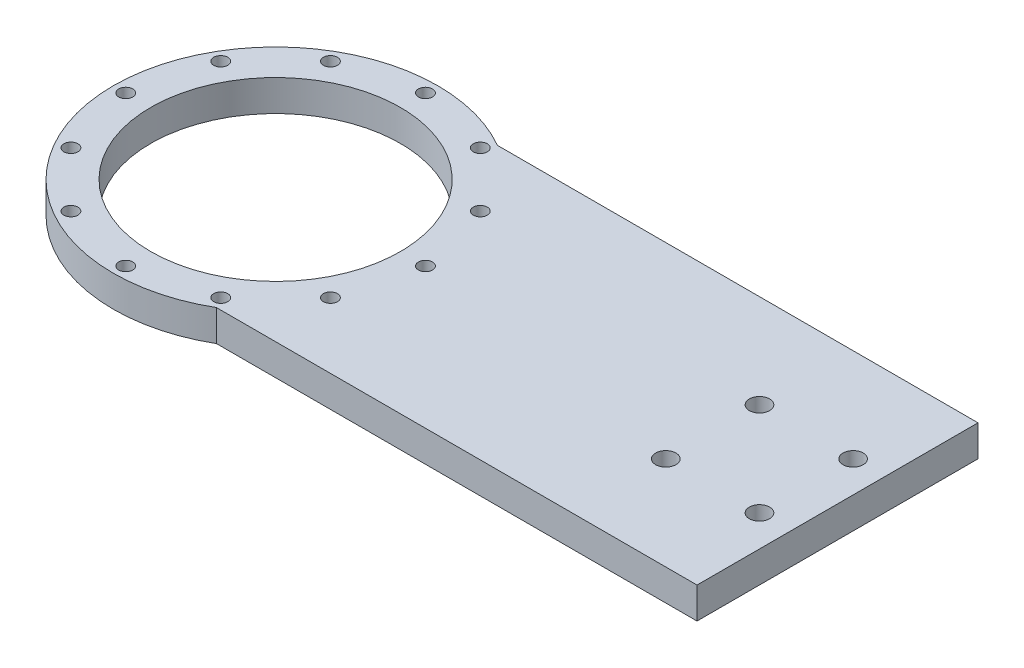
SolidWorks part; units mm, degrees
ref_plane "Front Plane" through (0, 0, 0) normal (0, 0, 1) x (1, 0, 0)
ref_plane "Top Plane" through (0, 0, 0) normal (0, 1, 0) x (1, 0, 0)
ref_plane "Right Plane" through (0, 0, 0) normal (1, 0, 0) x (0, 0, -1)
sketch "Sketch1" plane through (0, 0, 0) normal (0, 1, 0) x (1, 0, 0)
  circle A0 centre (0, 0) radius 52
  dimension "D1" = 104
extrude "Boss-Extrude1" add sketch "Sketch1" along normal blind 10
sketch "Sketch2" plane through (0, 0, 0) normal (0, 1, 0) x (1, 0, 0)
  line L0 (180, -45) -> (0, -45)
  line L1 (180, -45) -> (180, 45)
  line L2 (0, -45) -> (0, 45)
  line L3 (180, 45) -> (0, 45)
  line L4 (0, 0) -> (180, 0) construction
  line L5 (90, -45) -> (90, 45) construction
  point P1 (90, 0)
  point P7 (0, 0)
  dimension "D1" = 180
  dimension "D2" = 90
extrude "Boss-Extrude2" add sketch "Sketch2" along normal blind 10
sketch "Sketch3" plane through (0, 10, 0) normal (0, 1, 0) x (1, 0, 0)
  circle A0 centre (0, 0) radius 40
  dimension "D1" = 80
extrude "Cut-Extrude1" cut sketch "Sketch3" against normal blind 10
sketch "Sketch4" plane through (0, 10, 0) normal (0, 1, 0) x (1, 0, 0)
  circle A0 centre (0, 0) radius 48 construction
  circle A1 centre (0, 48) radius 2.25
  dimension "D1" = 96
  dimension "D2" = 4.5
extrude "Cut-Extrude2" cut sketch "Sketch4" against normal through all
pattern_circular "CirPattern1" count 12 over 360 about axis through (0, 0, 0) along (0, 1, 0) of "Cut-Extrude2"
sketch "Sketch5" plane through (0, 10, 0) normal (0, 1, 0) x (1, 0, 0)
  line L0 (180, 0) -> (0, 0) construction
  line L1 (180, -45) -> (180, 45) construction
  line L3 (155, 0) -> (170, 0) construction
  line L4 (155, 0) -> (155, 15) construction
  line L5 (155, 15) -> (170, 15) construction
  line L6 (170, 0) -> (170, 15) construction
  line L7 (162.5, 15) -> (162.5, 0) construction
  line L8 (155, 7.5) -> (170, 7.5) construction
  circle A0 centre (170, 15) radius 3.25
  point P85 (162.5, 7.5)
  dimension "D4" = 6.5
  dimension "D1" = 15
  dimension "D2" = 15
  dimension "D3" = 10
extrude "Cut-Extrude3" cut sketch "Sketch5" against normal through all
pattern_linear "LPattern1" count 2 spacing 30 along (-1, 0, 0) count 2 spacing 30 along (0, 0, 1) of "Cut-Extrude3"
